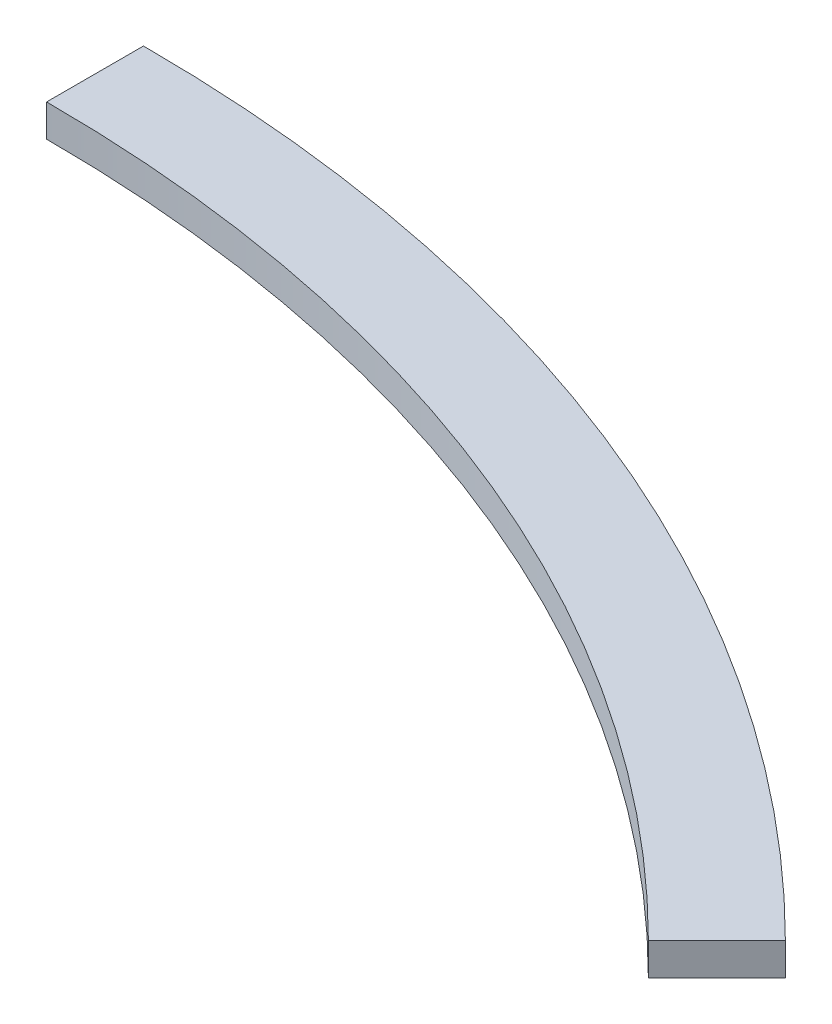
SolidWorks part; units mm, degrees
ref_plane "Front Plane" through (0, 0, 0) normal (0, 0, 1) x (1, 0, 0)
ref_plane "Top Plane" through (0, 0, 0) normal (0, 1, 0) x (1, 0, 0)
ref_plane "Right Plane" through (0, 0, 0) normal (1, 0, 0) x (0, 0, -1)
sketch "Sketch1" plane through (0, 0, 0) normal (0, 1, 0) x (1, 0, 0)
  line L0 (0, 0) -> (0, 450) construction
  line L1 (0, 450) -> (0, 480)
  line L2 (0, 0) -> (339.4113, 339.4113) construction
  line L3 (318.1981, 318.1981) -> (339.4113, 339.4113)
  arc A0 (0, 450) -> (318.1981, 318.1981) centre (0, 0) cw
  arc A1 (0, 480) -> (339.4113, 339.4113) centre (0, 0) cw
  dimension "D1" = 30
  dimension "D2" = 450
  dimension "D3" = 45
  dimension "D4" = 480
extrude "Boss-Extrude1" add sketch "Sketch1" along normal blind 10 contours A1 L1 A0 L3
